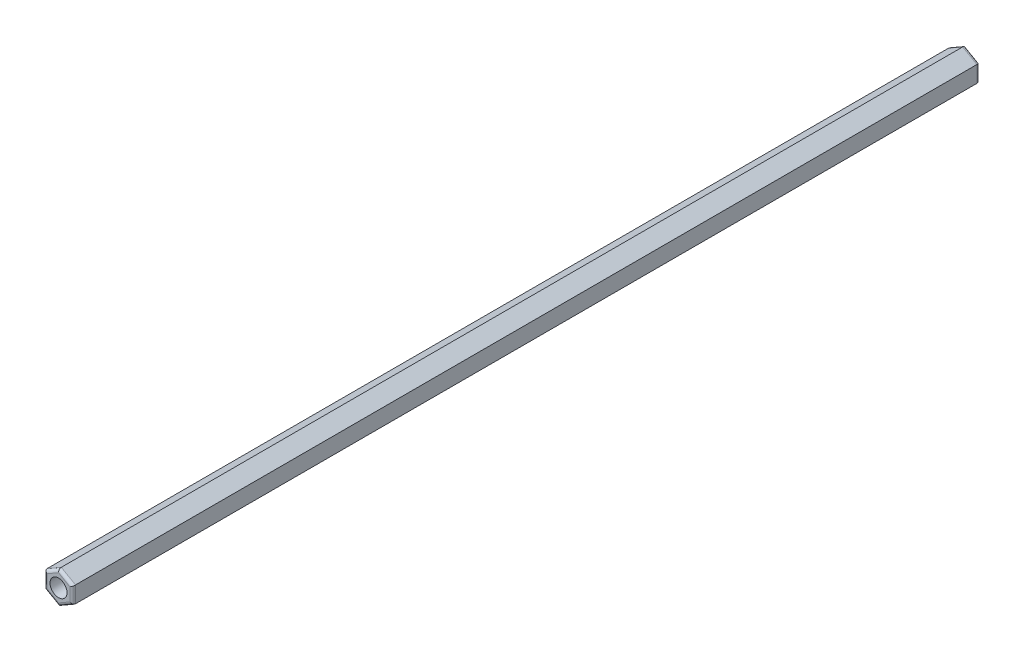
SolidWorks part; units mm, degrees
material "Inox rev"
ref_plane "Plano frontal" through (0, 0, 0) normal (0, 0, 1) x (1, 0, 0)
ref_plane "Plano superior" through (0, 0, 0) normal (0, 1, 0) x (1, 0, 0)
ref_plane "Plano direito" through (0, 0, 0) normal (1, 0, 0) x (0, 0, -1)
ref_plane "Plano1" through (0, 0, 0) normal (0, 0, -1) x (-1, 0, 0)
sketch "Esboço1" plane through (0, 0, 0) normal (0, 0, -1) x (-1, 0, 0)
  line L0 (67.5021, -1.4434) -> (70.0021, -2.8868)
  line L1 (70.0021, -2.8868) -> (72.5021, -1.4434)
  line L2 (72.5021, -1.4434) -> (72.5021, 1.4434)
  line L3 (72.5021, 1.4434) -> (70.0021, 2.8868)
  line L4 (70.0021, 2.8868) -> (67.5021, 1.4434)
  line L5 (67.5021, 1.4434) -> (67.5021, -1.4434)
extrude "Ressalto-extrusão1" add sketch "Esboço1" against normal blind 160
fillet "Filete1" radius 0.5 12 edges at (-71.2521, 2.1651, 0) (-72.5021, 0, 0) (-68.7521, 2.1651, 0) (-71.2521, -2.1651, 0) (-67.5021, 0, 0) (-68.7521, -2.1651, 0) (-71.2521, 2.1651, 160) (-72.5021, 0, 160) (-68.7521, 2.1651, 160) (-71.2521, -2.1651, 160) (-67.5021, 0, 160) (-68.7521, -2.1651, 160)
sketch "Esboço2" plane through (0, 0, 160) normal (0, 0, 1) x (1, 0, 0)
  circle A0 centre (-70.0021, 0) radius 1.5
  dimension "D1" = 3
extrude "Corte-extrusão1" cut sketch "Esboço2" against normal through all
